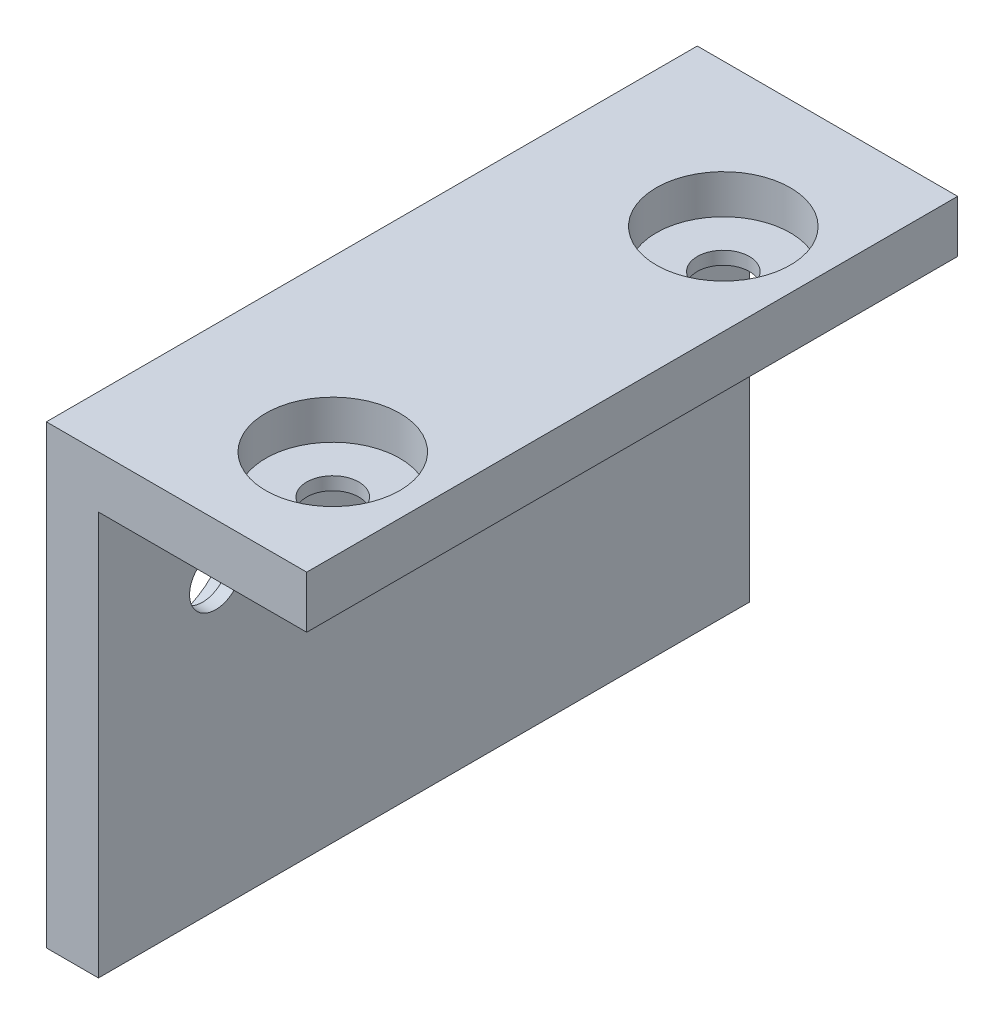
SolidWorks part; units mm, degrees
ref_plane "Plano frontal" through (0, 0, 0) normal (0, 0, 1) x (1, 0, 0)
ref_plane "Plano superior" through (0, 0, 0) normal (0, 1, 0) x (1, 0, 0)
ref_plane "Plano direito" through (0, 0, 0) normal (1, 0, 0) x (0, 0, -1)
sketch "Esboço1" plane through (0, 0, 0) normal (0, 0, 1) x (1, 0, 0)
  line L0 (0, 0) -> (16, 0)
  line L1 (16, 0) -> (16, 4)
  line L2 (16, 4) -> (-4, 4)
  line L3 (-4, 4) -> (-4, -31)
  line L4 (-4, -31) -> (0, -31)
  line L5 (0, -31) -> (0, 0)
  dimension "D1" = 4
  dimension "D2" = 20
  dimension "D3" = 35
extrude "Ressalto-extrusão1" add sketch "Esboço1" along normal blind 50
sketch "Esboço2" plane through (0, 4, 0) normal (0, 1, 0) x (1, 0, 0)
  line L0 (-6, -26) -> (14, -26) construction
  line L3 (16, -50) -> (-4, -50) construction
  line L4 (-4, -50) -> (-4, 0) construction
  circle A0 centre (9, -11) radius 5.15
  circle A1 centre (9, -41) radius 5.15
  dimension "D2" = 10.3
  dimension "D1" = 30
  dimension "D3" = 24
  dimension "D4" = 13
extrude "Corte-extrusão1" cut sketch "Esboço2" against normal blind 3
sketch "Esboço3" plane through (-4, 0, 0) normal (-1, 0, 0) x (0, 0, 1)
  line L0 (26, 4) -> (26, -31) construction
  line L1 (50, -31) -> (0, -31) construction
  line L2 (50, 4) -> (0, 4) construction
  line L3 (50, 4) -> (50, -31) construction
  circle A0 centre (11, -9) radius 5.15
  circle A1 centre (41, -9) radius 5.15
  point P21 (26, -13.5)
  dimension "D3" = 10.3
  dimension "D1" = 30
  dimension "D2" = 24
  dimension "D4" = 13
extrude "Corte-extrusão2" cut sketch "Esboço3" against normal blind 3
sketch "Esboço4" plane through (-1, 0, 0) normal (-1, 0, 0) x (0, 0, 1)
  circle A0 centre (11, -9) radius 2
  circle A1 centre (41, -9) radius 2
  dimension "D1" = 4
extrude "Corte-extrusão3" cut sketch "Esboço4" against normal blind 10
sketch "Esboço5" plane through (0, 1, 0) normal (0, 1, 0) x (1, 0, 0)
  circle A0 centre (9, -11) radius 2
  circle A1 centre (9, -41) radius 2
  dimension "D1" = 4
extrude "Corte-extrusão4" cut sketch "Esboço5" against normal blind 10
